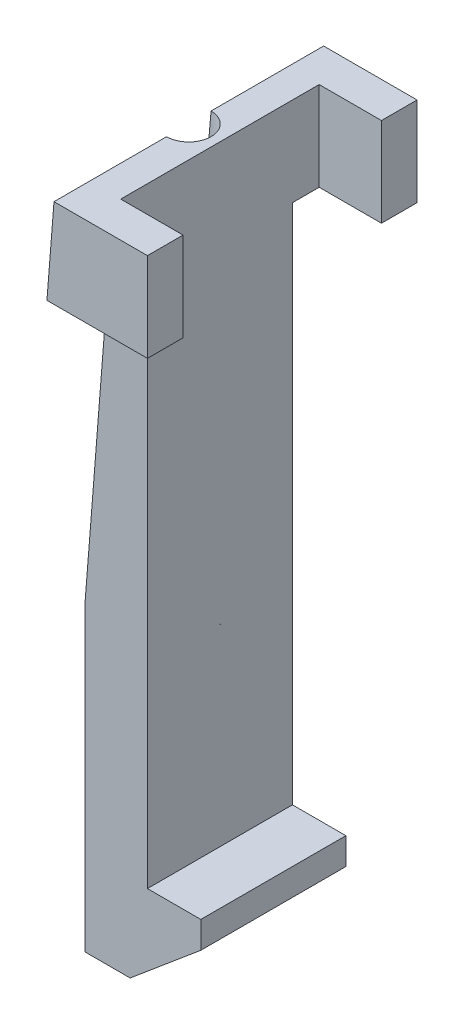
SolidWorks part; units mm, degrees
ref_plane "Front Plane" through (0, 0, 0) normal (0, 0, 1) x (1, 0, 0)
ref_plane "Top Plane" through (0, 0, 0) normal (0, 1, 0) x (1, 0, 0)
ref_plane "Right Plane" through (0, 0, 0) normal (1, 0, 0) x (0, 0, -1)
sketch "Sketch2" plane through (0, 0, 0) normal (0, 0, 1) x (1, 0, 0)
  line L0 (-0.5, 2.16) -> (-0.5, -4.7)
  line L1 (-0.5, -4.7) -> (0.1, -4.7)
  line L2 (0.5, -4.7) -> (-0.5, -4.7) construction
  line L3 (0.1, -4.7) -> (0.1, -5.0008)
  line L4 (0.1, -5.0008) -> (-0.6944, -5.6674)
  line L5 (-0.6944, -5.6674) -> (-1.2, -5.6674)
  line L6 (-1.2, -5.6674) -> (-1.2, 2.16)
  line L7 (-1.2, 2.16) -> (-0.5, 2.16)
  line L12 (0.5, 2.16) -> (-0.5, 2.16) construction
  dimension "D1" = 0.6
  dimension "D2" = 0.7
  dimension "D3" = 140
extrude "Boss-Extrude2" add sketch "Sketch2" against normal offset from surface (1.63 mm away) 0.2 from offset 0.2 offset against normal yes
sketch "Sketch5" plane through (0, 0, -0.2) normal (0, 0, 1) x (1, 0, 0)
  line L0 (-1.2, 2.16) -> (-1.2, -5.6674) construction
  line L1 (-0.5, 2.16) -> (-1.2, 2.16)
  line L2 (-0.5, 2.16) -> (-0.5, 1.16)
  line L3 (-0.5, 1.16) -> (-1.2, 1.16)
  line L4 (-1.2, 2.16) -> (-1.2, 1.16)
  dimension "D1" = 1
extrude "Boss-Extrude4" add sketch "Sketch5" along a picked direction on the side of the normal blind 0.7 contours L4 L3 L2 L1
sketch "Sketch6" plane through (-0.5, 0, 0) normal (1, 0, 0) x (0, 0, -1)
  line L0 (1.83, 2.16) -> (-0.5, 2.16) construction
  line L1 (-0.5, 1.16) -> (-0.1, 1.16)
  line L2 (-0.5, 1.16) -> (-0.5, 2.16)
  line L3 (-0.5, 2.16) -> (-0.1, 2.16)
  line L4 (-0.1, 1.16) -> (-0.1, 2.16)
  line L5 (0, -0.38) -> (0, 2.16) construction
  dimension "D1" = 0.1
extrude "Boss-Extrude5" add sketch "Sketch6" along normal blind 0.7 contours L2 L3 L4 L1
ref_plane "Plane1" through (0, 0, -1.015) normal (0, 0, 1) x (1, 0, 0)
mirror "Mirror1" about plane through (0, 0, -1.015) normal (0, 0, 1) of "Boss-Extrude4", "Boss-Extrude5"
sketch "Sketch3" plane through (0, 0, -0.2) normal (0, 0, 1) x (1, 0, 0)
  line L0 (-0.85, 2.16) -> (-1.2, -2.2537)
  line L1 (-1.2, 2.16) -> (-0.85, 2.16) construction
  line L2 (-0.85, 2.16) -> (-0.5, 2.16) construction
  line L3 (-1.2, -2.2537) -> (-1.2, 2.16)
  line L4 (-1.2, 2.16) -> (-0.85, 2.16)
  line L7 (-1.2, 1.16) -> (-1.2, -5.6674) construction
  line L8 (0.2, 2.16) -> (-1.2, 2.16) construction
  line L9 (-0.5, 2.16) -> (-0.5, 1.16) construction
  line L10 (0.2, 1.16) -> (-1.2, 1.16) construction
extrude "Cut-Extrude1" cut sketch "Sketch3" against normal through all and the other way blind 0.7
sketch "Sketch7" plane through (0, 2.16, 0) normal (0, 1, 0) x (1, 0, 0)
  line L0 (-0.85, -0.5) -> (-0.85, 2.53) construction
  circle A0 centre (-0.85, 1.015) radius 0.25
  dimension "D1" = 0.5
extrude "Cut-Extrude2" cut sketch "Sketch7" against normal through all contours A0
